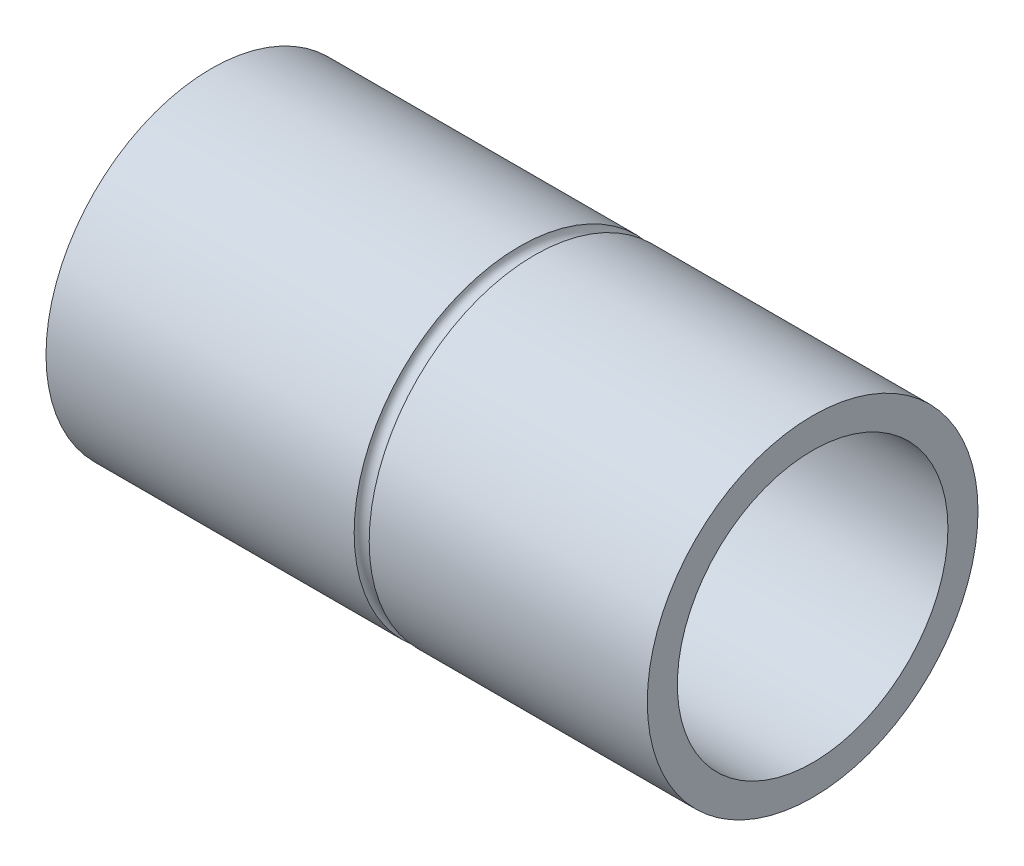
SolidWorks part; units mm, degrees
ref_plane "Front Plane" through (0, 0, 0) normal (0, 0, 1) x (1, 0, 0)
ref_plane "Top Plane" through (0, 0, 0) normal (0, 1, 0) x (1, 0, 0)
ref_plane "Right Plane" through (0, 0, 0) normal (1, 0, 0) x (0, 0, -1)
sketch "Sketch1" plane through (0, 0, 0) normal (1, 0, 0) x (0, 0, -1)
  circle A0 centre (0, 0) radius 55
extrude "Boss-Extrude1" add sketch "Sketch1" along normal blind 200
sketch "Sketch2" plane through (200, 0, 0) normal (1, 0, 0) x (0, 0, -1)
  circle A0 centre (0, 0) radius 45
extrude "Cut-Extrude1" cut sketch "Sketch2" against normal blind 190
sketch "Sketch3" plane through (0, 0, 0) normal (-1, 0, 0) x (0, 0, 1)
  circle A0 centre (0, 0) radius 17.5
extrude "Cut-Extrude2" cut sketch "Sketch3" against normal through all both and the other way through all
sketch "Sketch4" plane through (0, 0, 0) normal (-1, 0, 0) x (0, 0, 1)
  circle A0 centre (0, 34) radius 5
  circle A1 centre (0, -34) radius 5
extrude "Cut-Extrude3" cut sketch "Sketch4" against normal blind 2
sketch "Sketch5" plane through (0, 0, 0) normal (-1, 0, 0) x (0, 0, 1)
  circle A0 centre (0, 0) radius 22.5
extrude "Cut-Extrude4" cut sketch "Sketch5" against normal blind 2
sketch "Sketch13" plane through (0, 0, 0) normal (0, 1, 0) x (1, 0, 0)
  line L0 (-100, 0) -> (100, 0) construction
  point P4 (0, 0)
sketch3d "3DSketch5" plane through (0, 0, 0) normal (0, 0, 1) x (1, 0, 0)
  dimension "D1" = 105
sketch "Sketch57" plane through (105, 0, 0) normal (1, 0, 0) x (0, 0, -1)
  circle A0 centre (0, 0) radius 55
sweep "Cut-Sweep1" cut path "Sketch57" circular profile diameter 5 parameters "D3"=5
sketch "Sketch58" plane through (2, 0, 0) normal (-1, 0, 0) x (0, 0, 1)
  circle A0 centre (0, 34) radius 2.5
  circle A1 centre (0, -34) radius 2.5
extrude "Cut-Extrude5" cut sketch "Sketch58" against normal blind 2
